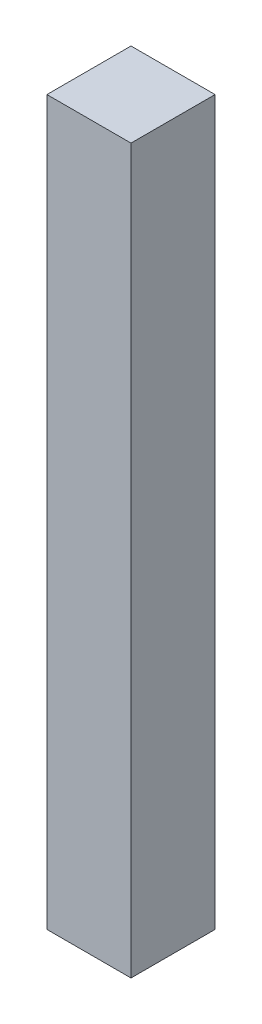
SolidWorks part; units mm, degrees
ref_plane "Front Plane" through (0, 0, 0) normal (0, 0, 1) x (1, 0, 0)
ref_plane "Top Plane" through (0, 0, 0) normal (0, 1, 0) x (1, 0, 0)
ref_plane "Right Plane" through (0, 0, 0) normal (1, 0, 0) x (0, 0, -1)
sketch "Sketch1" plane through (0, 0, 0) normal (0, 1, 0) x (1, 0, 0)
  line L1 (0, 0) -> (10, 0)
  line L2 (0, 0) -> (0, -10)
  line L3 (0, -10) -> (10, -10)
  line L4 (10, 0) -> (10, -10)
  point P5 (5, 0)
  dimension "D1" = 10
  dimension "D2" = 10
extrude "Boss-Extrude1" add sketch "Sketch1" along normal blind 86
